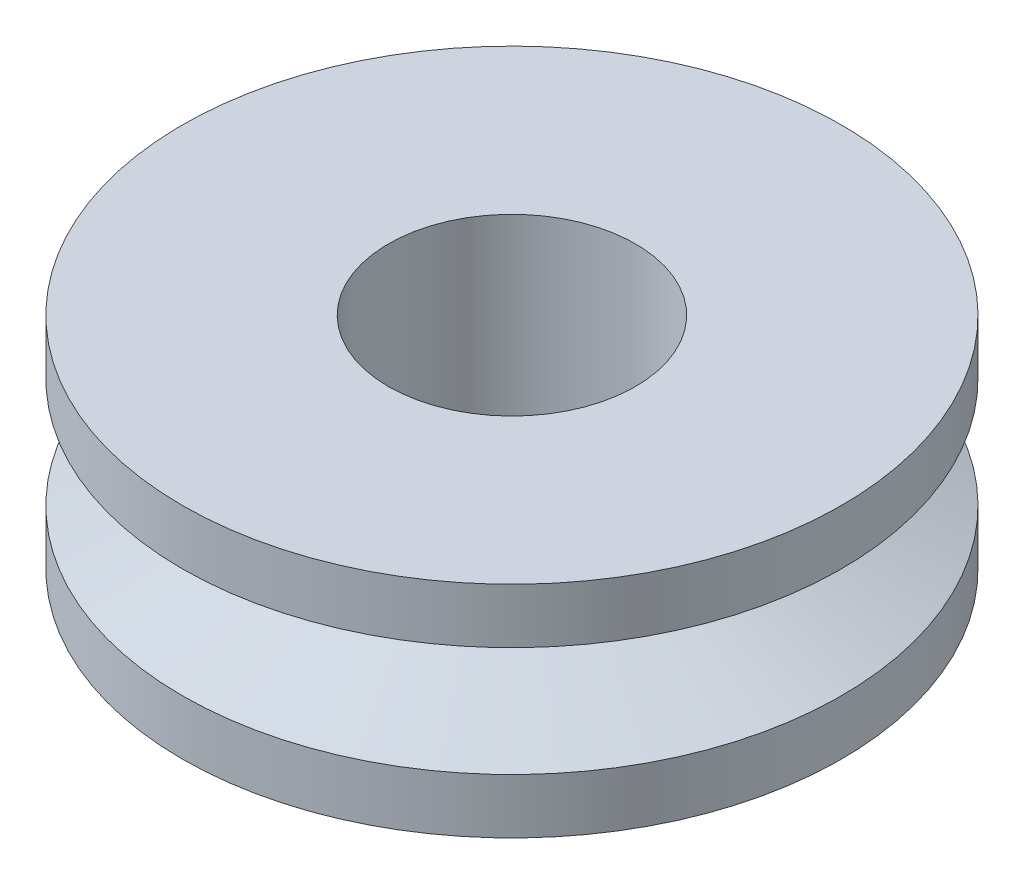
SolidWorks part; units mm, degrees
ref_plane "Front Plane" through (0, 0, 0) normal (0, 0, 1) x (1, 0, 0)
ref_plane "Top Plane" through (0, 0, 0) normal (0, 1, 0) x (1, 0, 0)
ref_plane "Right Plane" through (0, 0, 0) normal (1, 0, 0) x (0, 0, -1)
sketch "Sketch2" plane through (0, 0, 0) normal (0, 0, 1) x (1, 0, 0)
  line L0 (0, 14.3204) -> (0, -14.3204) construction
  line L1 (0, 0) -> (9.375, 0) construction
  line L9 (15, 5) -> (5.625, 5)
  line L10 (5.625, 5) -> (5.625, -5)
  line L11 (5.625, -5) -> (15, -5)
  line L12 (15, 5) -> (15, 2.5)
  line L13 (15, 2.5) -> (8.9645, 0)
  line L14 (8.9645, 0) -> (15, -2.5)
  line L15 (15, -2.5) -> (15, -5)
  point P4 (0, 0)
  point P8 (0, 0)
  point P14 (0, 0)
  point P15 (0, 0)
  point P16 (0, 0)
  dimension "D1" = 10
  dimension "D2" = 5.625
  dimension "D3" = 45
  dimension "D4" = 2.5
  dimension "D5" = 15
revolve "Revolve2" add sketch "Sketch2" angle 360 about L0
